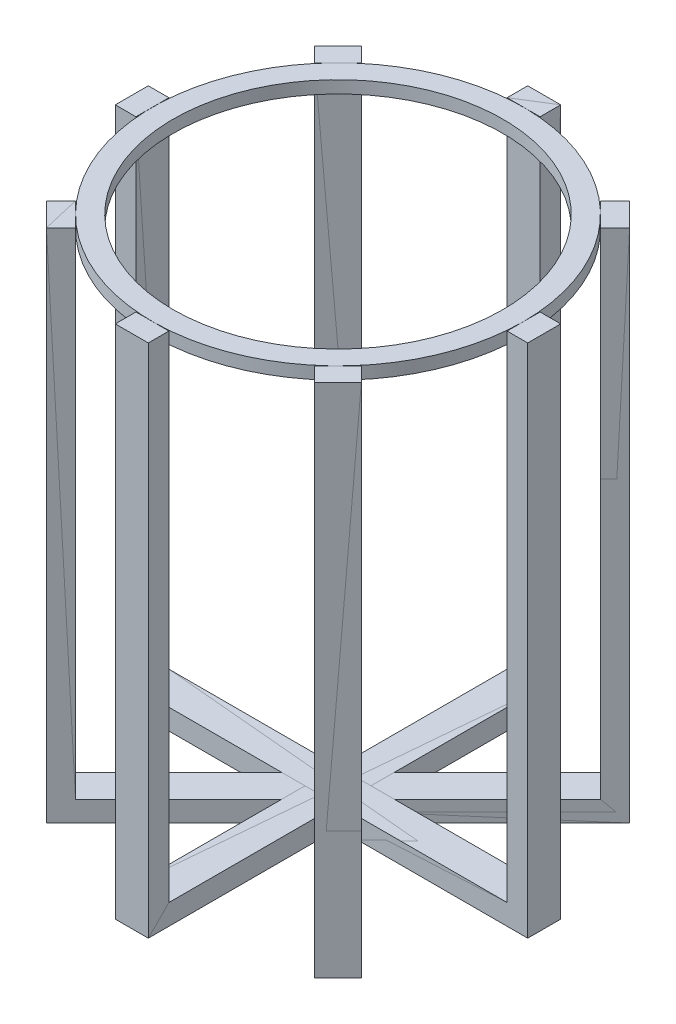
SolidWorks part; units mm, degrees
ref_plane "Front Plane" through (0, 0, 0) normal (0, 0, 1) x (1, 0, 0)
ref_plane "Top Plane" through (0, 0, 0) normal (0, 1, 0) x (1, 0, 0)
ref_plane "Right Plane" through (0, 0, 0) normal (1, 0, 0) x (0, 0, -1)
sketch "Sketch1" plane through (0, 0, 0) normal (0, 1, 0) x (1, 0, 0)
  circle A0 centre (0, 0) radius 40
  dimension "D1" = 80
extrude "Extrude-Thin1" add sketch "Sketch1" along normal blind 3 thin
sketch "Sketch2" plane through (0, 0, 0) normal (0, 0, 1) x (1, 0, 0)
  line L0 (45, 3) -> (45, -117)
  line L2 (-45, 3) -> (-45, -117)
  line L4 (-45, -117) -> (45, -117)
  dimension "D1" = 120
extrude "Extrude-Thin2" add sketch "Sketch2" along normal mid plane 8 separate body thin thin type one direction wall 5
pattern_circular "CirPattern4" count 8 over 360 about axis through (0, 0, 0) along (0, 1, 0) of bodies 102
